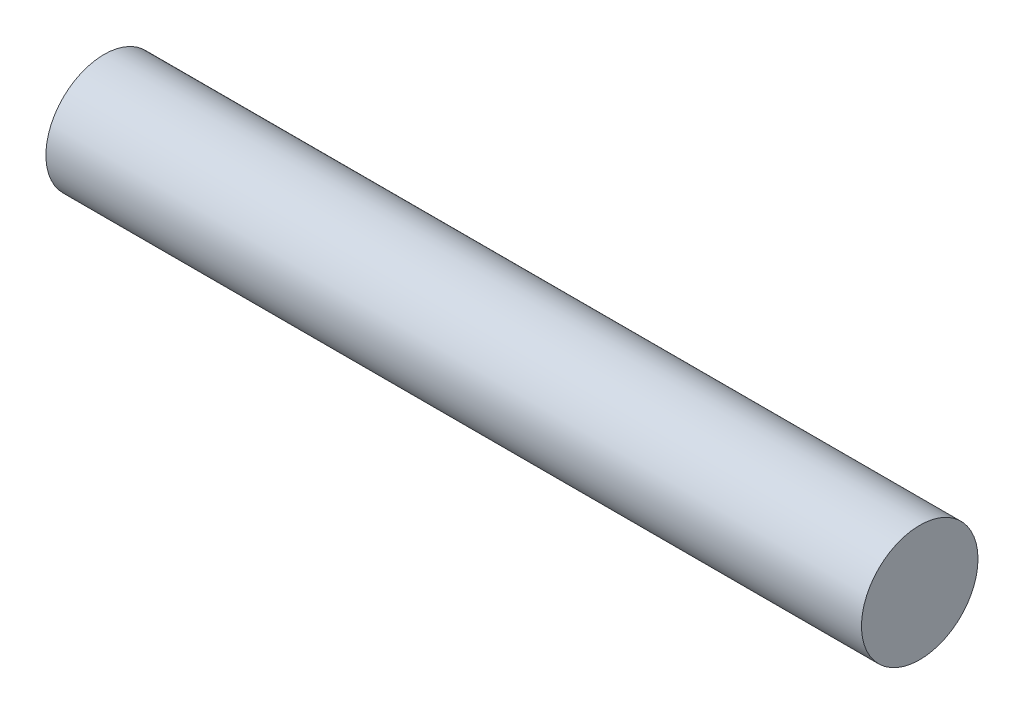
SolidWorks part; units mm, degrees
material "Plain Carbon Steel"
ref_plane "Front Plane" through (0, 0, 0) normal (0, 0, 1) x (1, 0, 0)
ref_plane "Top Plane" through (0, 0, 0) normal (0, 1, 0) x (1, 0, 0)
ref_plane "Right Plane" through (0, 0, 0) normal (1, 0, 0) x (0, 0, -1)
sketch "Sketch1" plane through (0, 0, 0) normal (1, 0, 0) x (0, 0, -1)
  circle A0 centre (0, 0) radius 19.05
extrude "Boss-Extrude1" add sketch "Sketch1" along normal mid plane 266.7
